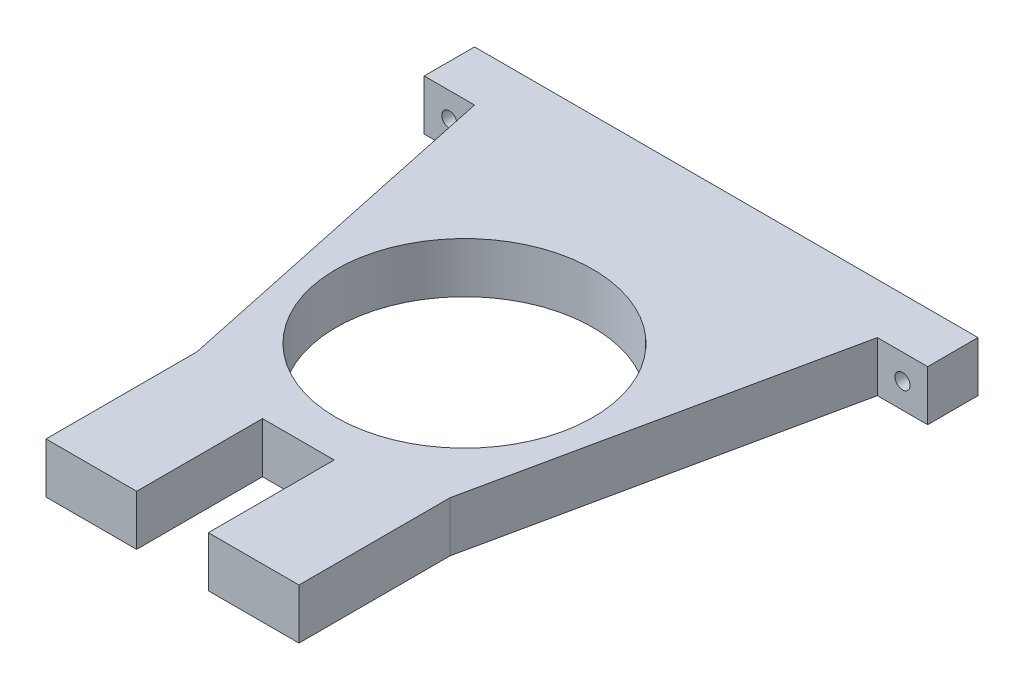
SolidWorks part; units mm, degrees
material "ABS"
ref_plane "Front Plane" through (0, 0, 0) normal (0, 0, 1) x (1, 0, 0)
ref_plane "Top Plane" through (0, 0, 0) normal (0, 1, 0) x (1, 0, 0)
ref_plane "Right Plane" through (0, 0, 0) normal (1, 0, 0) x (0, 0, -1)
sketch "Croquis1" plane through (0, 0, 0) normal (0, 1, 0) x (1, 0, 0)
  line L0 (50, 0) -> (-50, 0)
  line L1 (-50, 0) -> (-50, -10)
  line L2 (-50, -10) -> (-40, -10)
  line L3 (-40, -10) -> (-25.121, -80)
  line L4 (-25.121, -80) -> (-25.121, -110)
  line L5 (-25.121, -110) -> (-7.121, -110)
  line L6 (-7.121, -110) -> (-7.121, -85)
  line L7 (-7.121, -85) -> (7.121, -85)
  line L8 (7.121, -85) -> (7.121, -110)
  line L9 (7.121, -110) -> (25.121, -110)
  line L10 (25.121, -110) -> (25.121, -80)
  line L11 (25.121, -80) -> (40, -10)
  line L12 (40, -10) -> (50, -10)
  line L13 (50, -10) -> (50, 0)
  line L14 (0, 0) -> (0, -52) construction
  line L15 (25.121, -80) -> (-25.121, -80) construction
  line L16 (0, -85) -> (0, -52) construction
  line L17 (-7.121, -110) -> (7.121, -110) construction
  circle A0 centre (0, -52) radius 25.5
  point P3 (-25.5, -70)
  point P4 (0, 0)
  dimension "D5" = 51
  dimension "D1" = 100
  dimension "D2" = 10
  dimension "D3" = 52
  dimension "D4" = 10
  dimension "D6" = 102
  dimension "D7" = 18
  dimension "D8" = 102
  dimension "D9" = 70
  dimension "D10" = 30
  dimension "D11" = 25
extrude "Saliente-Extruir1" add sketch "Croquis1" along normal blind 10 contours L12 L13 L0 L1 L2 L3 L4 L5 L8 L7 L6 L9 L10 L11 A0
sketch "Croquis2" plane through (0, 0, 10) normal (0, 0, 1) x (1, 0, 0)
  line L0 (-50, 5) -> (-45, 5) construction
  line L1 (-50, 10) -> (-50, 0) construction
  line L2 (50, 5) -> (45, 5) construction
  line L4 (-45, 10) -> (-45, 5) construction
  line L5 (-50, 10) -> (-40, 10) construction
  line L6 (50, 10) -> (50, 0) construction
  line L8 (45, 10) -> (45, 5) construction
  line L9 (40, 10) -> (50, 10) construction
  circle A0 centre (-45, 5) radius 1.5
  circle A1 centre (45, 5) radius 1.5
  dimension "D1" = 3
  dimension "D2" = 3
extrude "Cortar-Extruir1" cut sketch "Croquis2" against normal up to next
